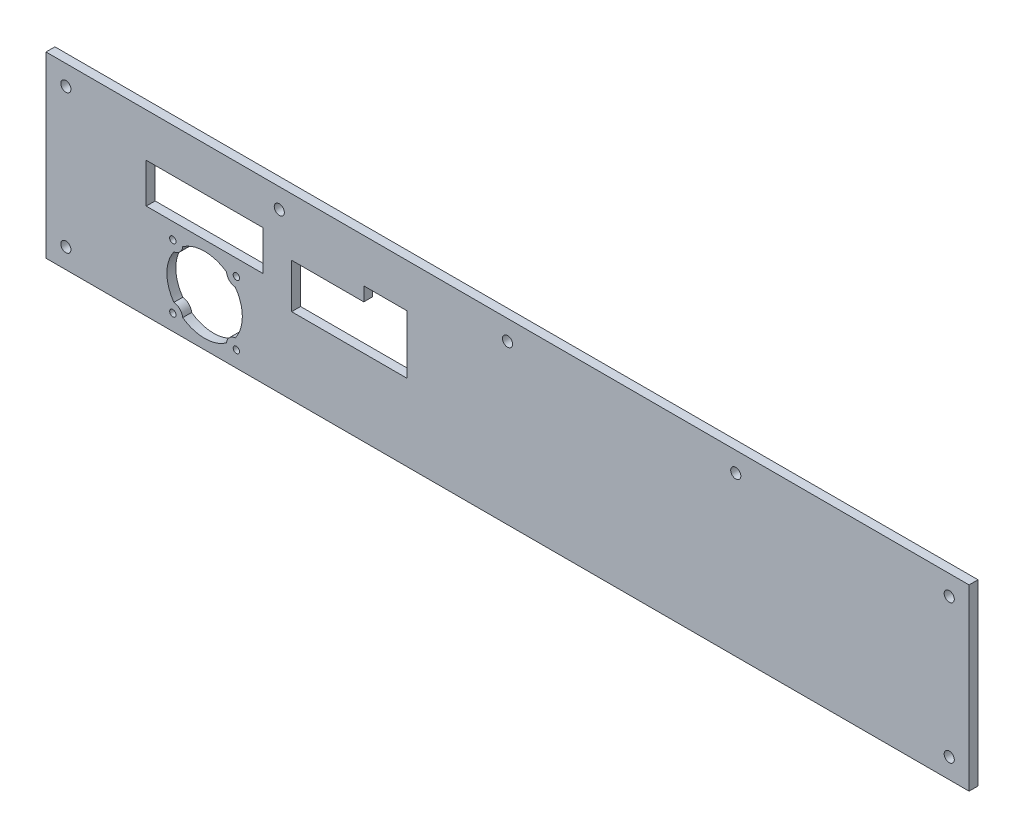
SolidWorks part; units mm, degrees
material "Acrylic (Medium-high impact)"
ref_plane "Front Plane" through (0, 0, 0) normal (0, 0, 1) x (1, 0, 0)
ref_plane "Top Plane" through (0, 0, 0) normal (0, 1, 0) x (1, 0, 0)
ref_plane "Right Plane" through (0, 0, 0) normal (1, 0, 0) x (0, 0, -1)
sketch "Sketch1" plane through (0, 0, 0) normal (0, 0, 1) x (1, 0, 0)
  line L0 (-222.5, 45) -> (-222.5, -45) construction
  line L1 (-232.5, -45) -> (232.5, -45)
  line L2 (-232.5, -45) -> (-232.5, 45)
  line L3 (-232.5, 45) -> (232.5, 45)
  line L4 (232.5, -45) -> (232.5, 45)
  line L5 (-232.5, -45) -> (232.5, 45) construction
  line L6 (-232.5, 45) -> (232.5, -45) construction
  line L7 (0, 45) -> (0, -45) construction
  line L8 (-232.5, 35) -> (2.55, 35) construction
  circle A0 centre (-222.5, 35) radius 2.55
  circle A1 centre (-222.5, -35) radius 2.55
  circle A2 centre (0, 35) radius 2.55
  circle A3 centre (-114.975, 35) radius 2.55
  circle A4 centre (222.5, -35) radius 2.55
  circle A5 centre (222.5, 35) radius 2.55
  circle A6 centre (114.975, 35) radius 2.55
  point P0 (0, 0)
  point P17 (-114.975, 35)
  dimension "D4" = 5.1
  dimension "D5" = 10
  dimension "D6" = 10
  dimension "D7" = 10
  dimension "D1" = 465
  dimension "D2" = 90
  dimension "D3" = 10
extrude "Boss-Extrude1" add sketch "Sketch1" along normal mid plane 4.4958
sketch "Sketch2" plane through (0, 0, 2.2479) normal (0, 0, 1) x (1, 0, 0)
  line L0 (-54.2, 13) -> (-104.2, 13) construction
  line L1 (-108.7472, 16) -> (-72.4223, 16)
  line L2 (-108.7472, 16) -> (-108.7472, -6.43)
  line L3 (-108.7472, -6.43) -> (-50.5423, -6.43)
  line L4 (-50.5423, 23) -> (-50.5423, -6.43)
  line L5 (-104.7472, 2.27) -> (-104.7472, 6.02) construction
  line L6 (-53.5423, 11.4) -> (-53.5423, -2.1) construction
  line L7 (-74.6342, -3.43) -> (-85.7342, -3.43) construction
  line L8 (-69.4223, 11.4) -> (-69.4223, -2.1) construction
  line L9 (-127.2, 23) -> (-178, 23) construction
  line L10 (-182, 23) -> (-123.2, 23)
  line L11 (-50.5423, 23) -> (-72.4223, 23)
  line L12 (-72.4223, 16) -> (-72.4223, 23)
  line L13 (-182, 23) -> (-182, 3)
  line L14 (-182, 3) -> (-123.2, 3)
  line L15 (-123.2, 23) -> (-123.2, 3)
  line L18 (-127.2, 21.4) -> (-127.2, 23) construction
  line L19 (-178, 21.4) -> (-178, 23) construction
  line L20 (-152.6, 3) -> (-152.6, -45) construction
  line L21 (-232.5, -45) -> (232.5, -45) construction
  line L23 (-168.6, -37) -> (-136.6, -37) construction
  line L24 (-168.6, -37) -> (-168.6, -5) construction
  line L25 (-168.6, -5) -> (-136.6, -5) construction
  line L26 (-136.6, -37) -> (-136.6, -5) construction
  line L27 (-168.6, -37) -> (-136.6, -5) construction
  line L28 (-168.6, -5) -> (-136.6, -37) construction
  line L29 (-172.6, -41) -> (-132.6, -41) construction
  line L30 (-172.6, -41) -> (-172.6, -1) construction
  line L31 (-172.6, -1) -> (-132.6, -1) construction
  line L32 (-132.6, -41) -> (-132.6, -1) construction
  line L33 (-172.6, -41) -> (-132.6, -1) construction
  line L34 (-172.6, -1) -> (-132.6, -41) construction
  arc A0 (-163.628, -36.472) -> (-141.5721, -36.472) centre (-152.6, -21) ccw
  circle A1 centre (-136.6, -5) radius 1.6
  circle A2 centre (-168.6, -5) radius 1.6
  circle A3 centre (-168.6, -37) radius 1.6
  circle A4 centre (-136.6, -37) radius 1.6
  arc A5 (-168.0721, -9.972) -> (-168.0721, -32.028) centre (-152.6, -21) ccw
  arc A6 (-141.5721, -5.528) -> (-137.128, -9.972) centre (-136.6, -5) ccw
  arc A7 (-141.5721, -5.528) -> (-163.628, -5.528) centre (-152.6, -21) ccw
  arc A8 (-137.128, -32.028) -> (-137.128, -9.972) centre (-152.6, -21) ccw
  arc A10 (-168.0721, -9.972) -> (-163.628, -5.528) centre (-168.6, -5) ccw
  arc A11 (-163.628, -36.472) -> (-168.0721, -32.028) centre (-168.6, -37) ccw
  arc A12 (-137.128, -32.028) -> (-141.5721, -36.472) centre (-136.6, -37) ccw
  point P31 (-152.6, -21)
  dimension "D14" = 3.2
  dimension "D15" = 38
  dimension "D16" = 5
  dimension "D1" = 3
  dimension "D2" = 4
  dimension "D3" = 3
  dimension "D4" = 3
  dimension "D5" = 3
  dimension "D6" = 7
  dimension "D7" = 4
  dimension "D8" = 4
  dimension "D9" = 20
  dimension "D10" = 32
  dimension "D11" = 32
  dimension "D12" = 40
  dimension "D13" = 40
extrude "Cut-Extrude1" cut sketch "Sketch2" against normal up to next
